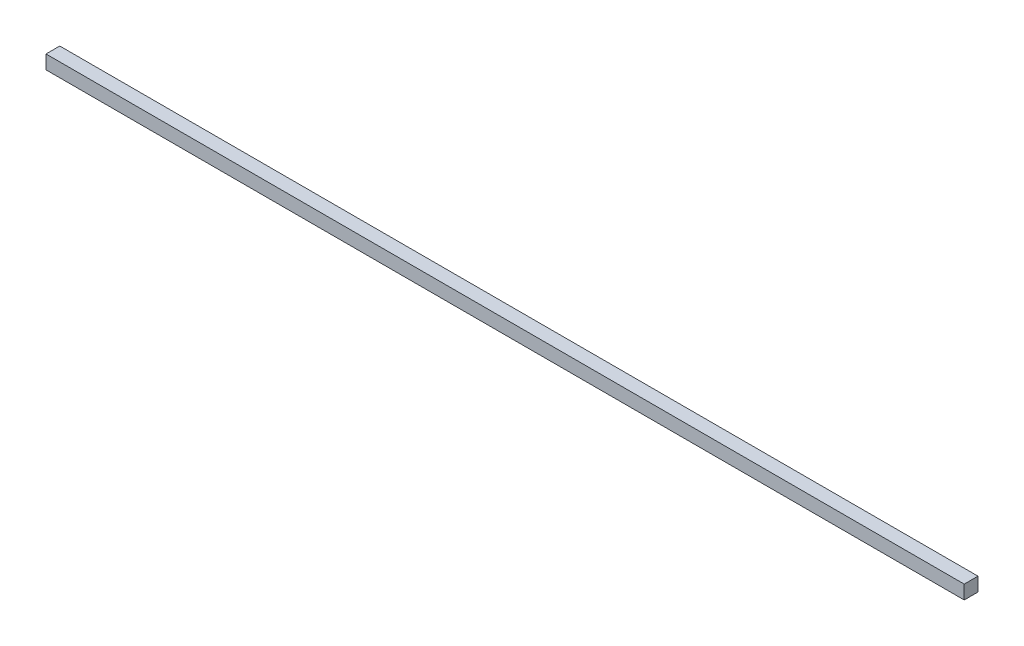
SolidWorks part; units mm, degrees
ref_plane "Спереди" through (0, 0, 0) normal (0, 0, 1) x (1, 0, 0)
ref_plane "Сверху" through (0, 0, 0) normal (0, 1, 0) x (1, 0, 0)
ref_plane "Справа" through (0, 0, 0) normal (1, 0, 0) x (0, 0, -1)
sketch "Эскиз1" plane through (0, 0, 0) normal (0, 1, 0) x (1, 0, 0)
  line L1 (0, 0) -> (2000, 0)
  line L2 (0, 0) -> (0, 30)
  line L3 (0, 30) -> (2000, 30)
  line L4 (2000, 0) -> (2000, 30)
extrude "Бобышка-Вытянуть1" add sketch "Эскиз1" along normal blind 30
